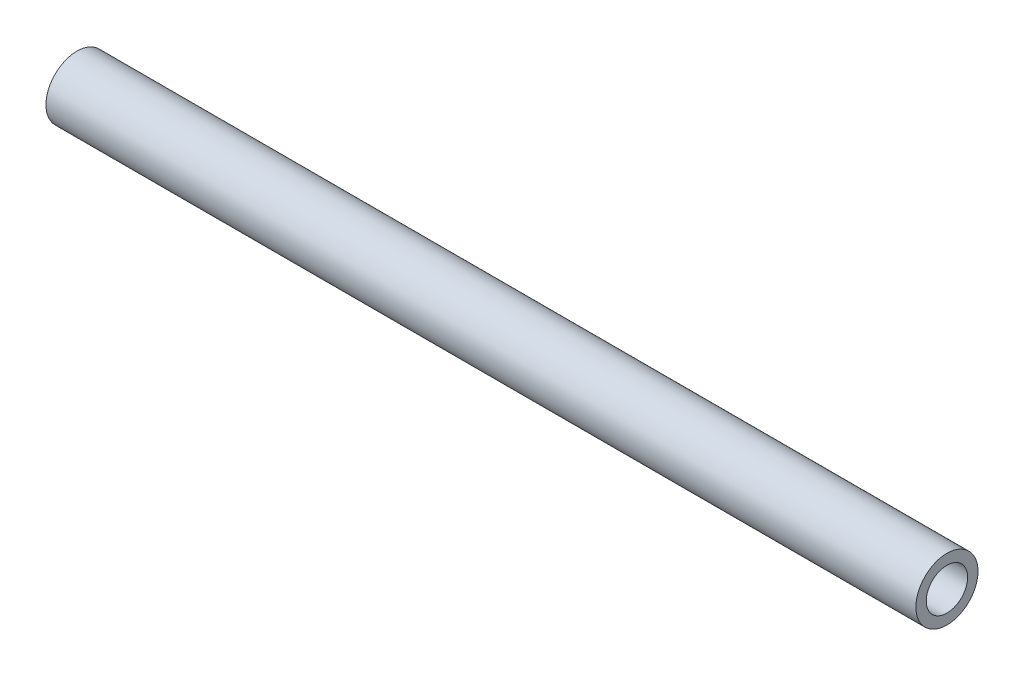
SolidWorks part; units mm, degrees
material "NEOPRENE"
ref_plane "Front Plane" through (0, 0, 0) normal (0, 0, 1) x (1, 0, 0)
ref_plane "Top Plane" through (0, 0, 0) normal (0, 1, 0) x (1, 0, 0)
ref_plane "Right Plane" through (0, 0, 0) normal (1, 0, 0) x (0, 0, -1)
sketch "Sketch1" plane through (0, 0, 0) normal (1, 0, 0) x (0, 0, -1)
  circle A0 centre (0, 0) radius 6.35
  circle A1 centre (0, 0) radius 9.525
  dimension "D1" = 12.7
  dimension "D2" = 19.05
extrude "Boss-Extrude1" add sketch "Sketch1" along normal blind 266.7
